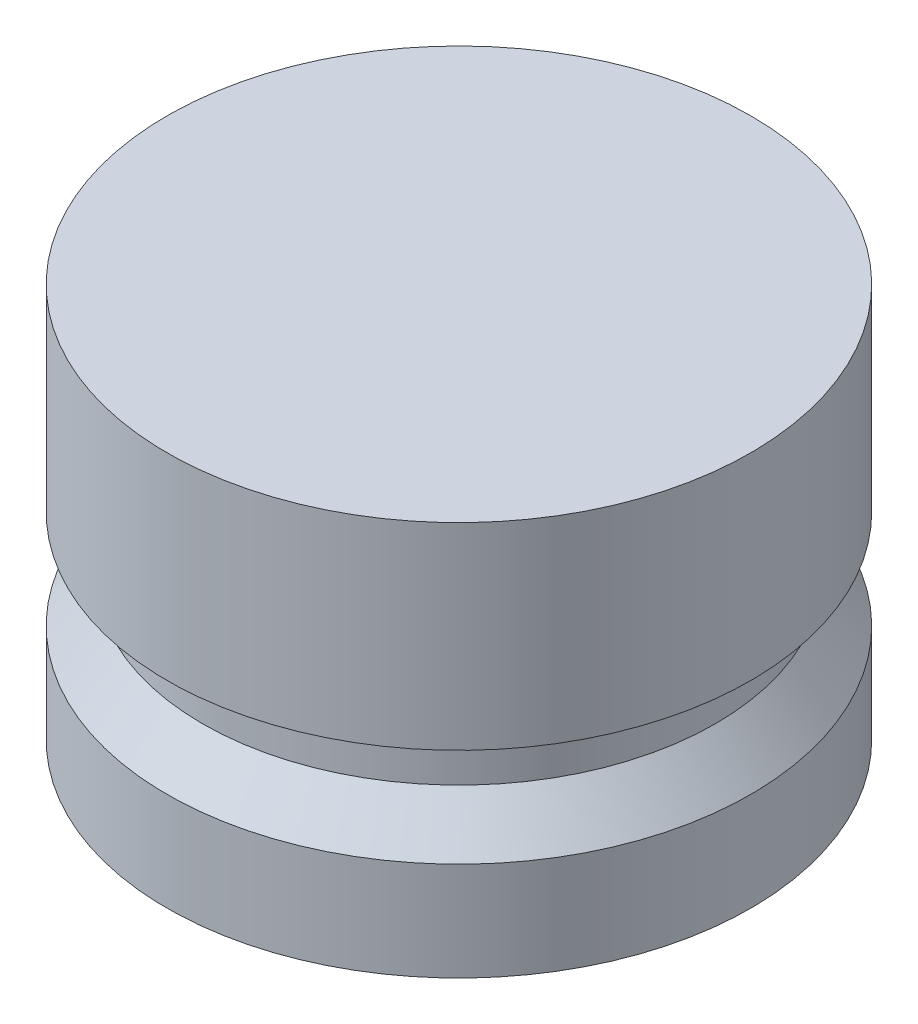
SolidWorks part; units mm, degrees
ref_plane "Front Plane" through (0, 0, 0) normal (0, 0, 1) x (1, 0, 0)
ref_plane "Top Plane" through (0, 0, 0) normal (0, 1, 0) x (1, 0, 0)
ref_plane "Right Plane" through (0, 0, 0) normal (1, 0, 0) x (0, 0, -1)
sketch "Sketch1" plane through (0, 0, 0) normal (0, 0, 1) x (1, 0, 0)
  line L0 (0, 0) -> (0, 12.7) construction
  line L1 (0, 0) -> (-9.398, 0)
  line L2 (-9.398, 0) -> (-9.398, 3.175)
  line L4 (-8.255, 4.572) -> (-8.255, 6.35)
  line L5 (-8.255, 6.35) -> (-9.398, 6.35)
  line L6 (-9.398, 6.35) -> (-9.398, 12.7)
  line L7 (-9.398, 12.7) -> (0, 12.7)
  line L8 (-9.525, 16.6801) -> (-9.525, -9.6051) construction
  line L9 (0, 0) -> (0, 12.7)
  line L10 (-8.255, 4.572) -> (-9.398, 3.175)
  dimension "D1" = 12.7
  dimension "D2" = 9.398
  dimension "D3" = 1.778
  dimension "D4" = 3.175
  dimension "D5" = 9.525
  dimension "D6" = 8.255
  dimension "D7" = 6.35
revolve "Revolve1" add sketch "Sketch1" angle 360 about L9
